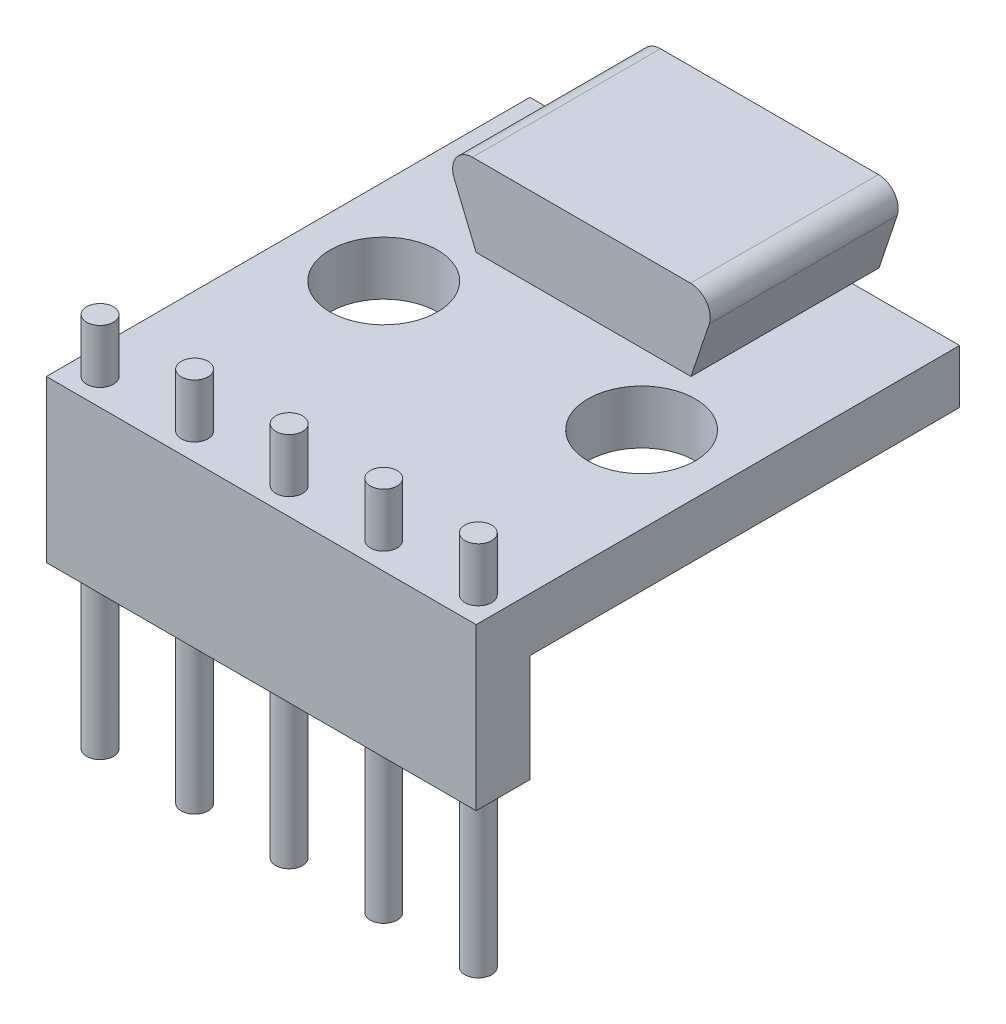
SolidWorks part; units mm, degrees
ref_plane "Front Plane" through (0, 0, 0) normal (0, 0, 1) x (1, 0, 0)
ref_plane "Top Plane" through (0, 0, 0) normal (0, 1, 0) x (1, 0, 0)
ref_plane "Right Plane" through (0, 0, 0) normal (1, 0, 0) x (0, 0, -1)
sketch "Sketch1" plane through (0, 0, 0) normal (0, 1, 0) x (1, 0, 0)
  line L1 (0, 0) -> (12.7, 0)
  line L2 (0, 0) -> (0, -14.2875)
  line L3 (0, -14.2875) -> (12.7, -14.2875)
  line L4 (12.7, 0) -> (12.7, -14.2875)
  circle A0 centre (10.16, -6.858) radius 1.5875
  circle A1 centre (2.54, -6.858) radius 1.5875
  dimension "D3" = 3.175
  dimension "D6" = 10.16
  dimension "D1" = 12.7
  dimension "D2" = 14.2875
  dimension "D4" = 6.858
  dimension "D5" = 10.16
extrude "Boss-Extrude1" add sketch "Sketch1" against normal blind 1.5875
sketch "Sketch2" plane through (0, 0, 14.2875) normal (0, 0, 1) x (1, 0, 0)
  line L0 (12.7, -1.5875) -> (12.7, 0) construction
  line L1 (0, -1.5875) -> (12.7, -1.5875)
  line L2 (0, -1.5875) -> (0, -4.7625)
  line L3 (0, -4.7625) -> (12.7, -4.7625)
  line L4 (12.7, -1.5875) -> (12.7, -4.7625)
  dimension "D1" = 3.175
extrude "Boss-Extrude2" add sketch "Sketch2" against normal blind 1.5875
sketch "Sketch3" plane through (0, 0, 0) normal (0, 1, 0) x (1, 0, 0)
  line L0 (0, -14.2875) -> (12.7, -14.2875) construction
  line L1 (0, 0) -> (0, -14.2875) construction
  circle A0 centre (0.7937, -13.4938) radius 0.3969
  circle A1 centre (3.5877, -13.4938) radius 0.3969
  circle A2 centre (6.3818, -13.4938) radius 0.3969
  circle A3 centre (9.1758, -13.4938) radius 0.3969
  circle A4 centre (11.9697, -13.4938) radius 0.3969
  dimension "D1" = 0.7937
  dimension "D2" = 0.7937
  dimension "D3" = 0.7937
  dimension "D4" = 5
extrude "Cut-Extrude1" cut sketch "Sketch3" against normal through all
sketch "Sketch4" plane through (0, 0, 0) normal (0, 1, 0) x (1, 0, 0)
  circle A0 centre (0.7937, -13.4938) radius 0.3969
  circle A1 centre (3.5877, -13.4938) radius 0.3969
  circle A2 centre (6.3818, -13.4938) radius 0.3969
  circle A3 centre (9.1758, -13.4938) radius 0.3969
  circle A4 centre (11.9697, -13.4938) radius 0.3969
  dimension "D1" = 0.7937
  dimension "D2" = 5
extrude "Boss-Extrude3" add sketch "Sketch4" along normal blind 1.5875 and the other way blind 9.525
sketch "Sketch5" plane through (0, 0, 0) normal (0, 0, -1) x (-1, 0, 0)
  line L0 (-9.525, 0) -> (-10.0623, 1.6118)
  line L1 (-12.7, 0) -> (0, 0) construction
  line L2 (-9.5077, 2.3812) -> (-3.0652, 2.3812)
  line L3 (-2.5249, 1.5734) -> (-3.175, 0)
  line L4 (-3.175, 0) -> (-9.525, 0)
  line L5 (0, -1.5875) -> (0, 0) construction
  arc A0 (-10.0623, 1.6118) -> (-9.5077, 2.3812) centre (-9.5077, 1.7967) cw
  arc A1 (-3.0652, 2.3812) -> (-2.5249, 1.5734) centre (-3.0652, 1.7967) cw
  dimension "D2" = 6.35
  dimension "D3" = 3.175
  dimension "D4" = 2.3813
extrude "Boss-Extrude5" add sketch "Sketch5" against normal blind 4.7625 and the other way blind 0.7937
